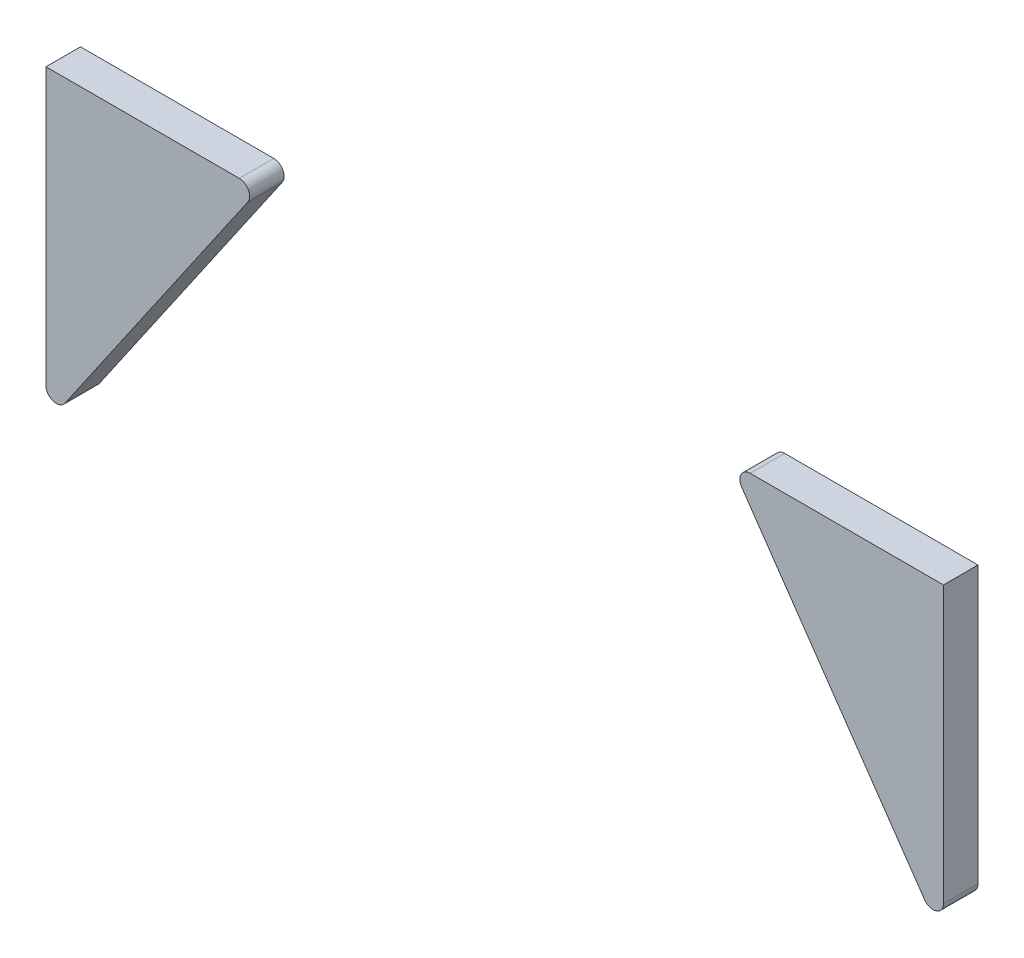
SolidWorks part; units mm, degrees
ref_plane "정면" through (0, 0, 0) normal (0, 0, 1) x (1, 0, 0)
ref_plane "윗면" through (0, 0, 0) normal (0, 1, 0) x (1, 0, 0)
ref_plane "우측면" through (0, 0, 0) normal (1, 0, 0) x (0, 0, -1)
sketch "스케치1" plane through (0, 0, 0) normal (0, 0, 1) x (1, 0, 0)
  line L0 (-128.1265, 0) -> (153.288, 0) construction
  line L1 (0, 85.781) -> (0, -92.7295) construction
  line L2 (-65, 10.0458) -> (-65, 50.0458)
  line L3 (-65, 50.0458) -> (-37, 50.0458)
  line L4 (-35.7644, 47.6953) -> (-62.2644, 9.1953)
  line L5 (65, 50.0458) -> (37, 50.0458)
  line L6 (65, 10.0458) -> (65, 50.0458)
  line L7 (35.7644, 47.6953) -> (62.2644, 9.1953)
  arc A0 (-35.7644, 47.6953) -> (-37, 50.0458) centre (-37, 48.5458) ccw
  arc A1 (-65, 10.0458) -> (-62.2644, 9.1953) centre (-63.5, 10.0458) ccw
  arc A2 (35.7644, 47.6953) -> (37, 50.0458) centre (37, 48.5458) cw
  arc A3 (65, 10.0458) -> (62.2644, 9.1953) centre (63.5, 10.0458) cw
  dimension "D1" = 1.5
  dimension "D2" = 40
  dimension "D3" = 28
  dimension "D4" = 65
extrude "보스-돌출1" add sketch "스케치1" along normal mid plane 5
